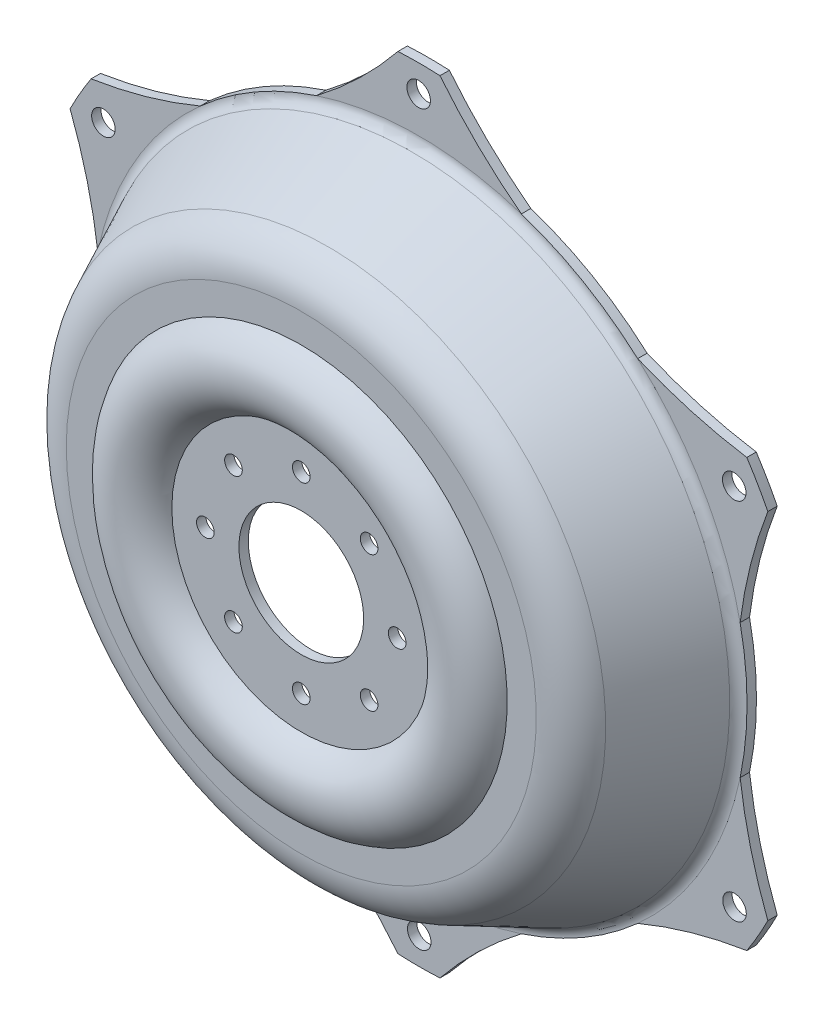
SolidWorks part; units mm, degrees
ref_plane "Front Plane" through (0, 0, 0) normal (0, 0, 1) x (1, 0, 0)
ref_plane "Top Plane" through (0, 0, 0) normal (0, 1, 0) x (1, 0, 0)
ref_plane "Right Plane" through (0, 0, 0) normal (1, 0, 0) x (0, 0, -1)
sketch "Sketch3" plane through (0, 0, 0) normal (0, 1, 0) x (1, 0, 0)
  line L16 (332.5, 100) -> (278.8208, 100)
  line L17 (262.5618, 89.723) -> (228.6217, 18.2702)
  line L18 (199.7168, 0) -> (169.6339, 0)
  line L19 (332.5, 92) -> (278.8208, 92)
  line L20 (269.788, 86.2906) -> (235.8479, 14.8377)
  line L21 (199.7168, -8) -> (175, -8)
  line L22 (0, 0) -> (0, -73.2185) construction
  line L23 (115.3661, 0) -> (53, 0)
  line L25 (53, -8) -> (53, 0)
  line L26 (324.5, 100) -> (278.8208, 100) construction
  line L27 (115.3661, 0) -> (61, 0) construction
  line L28 (110, -8) -> (53, -8)
  line L31 (332.5, 92) -> (332.5, 100)
  line L32 (61, 0) -> (61, 0) construction
  line L33 (324.5, 100) -> (324.5, 100) construction
  arc A6 (235.8479, 14.8377) -> (199.7168, -8) centre (199.7168, 32) cw
  arc A7 (269.788, 86.2906) -> (278.8208, 92) centre (278.8208, 82) cw
  arc A8 (262.5618, 89.723) -> (278.8208, 100) centre (278.8208, 82) cw
  arc A9 (228.6217, 18.2702) -> (199.7168, 0) centre (199.7168, 32) cw
  arc A10 (110, -8) -> (175, -8) centre (142.5, 8.4062) ccw
  arc A11 (115.3661, 0) -> (169.6339, 0) centre (142.5, 8.4062) ccw
  point P0 (142.5, -28)
  point P4 (225, -8)
  point P10 (272.5, 92)
  dimension "D8" = 20
  dimension "D9" = 40
  dimension "D10" = 10
  dimension "D1" = 53
  dimension "D2" = 110
  dimension "D3" = 175
  dimension "D4" = 50
  dimension "D5" = 100
  dimension "D6" = 60
  dimension "D7" = 89.5
  dimension "D11" = 8
  dimension "D13" = 47.5
  dimension "D12" = 8
revolve "Revolve1" add sketch "Sketch3" angle 360 about L22
sketch "Sketch5" plane through (0, 0, -100) normal (0, 0, 1) x (1, 0, 0)
  line L0 (0, 0) -> (0, 332.5) construction
  circle A0 centre (0, 0) radius 332.5 construction
  circle A1 centre (267.9147, 154.9582) radius 10
  arc A2 (296.4614, 150.5553) -> (269.8116, 0) centre (669.7531, 6.8428) ccw
  arc A3 (296.4614, 150.5553) -> (278.6154, 181.4654) centre (0, 0) ccw
  arc A4 (134.9058, 233.6637) -> (278.6154, 181.4654) centre (340.8025, 576.6018) ccw
  circle A5 centre (268.155, -154.5418) radius 10
  arc A6 (278.6154, -181.4654) -> (134.9058, -233.6637) centre (340.8025, -576.6018) ccw
  arc A7 (278.6154, -181.4654) -> (296.4614, -150.5553) centre (0, 0) ccw
  arc A8 (269.8116, 0) -> (296.4614, -150.5553) centre (669.7531, -6.8428) ccw
  circle A9 centre (0.2404, -309.5) radius 10
  arc A10 (-17.8459, -332.0207) -> (-134.9058, -233.6637) centre (-328.9505, -583.4445) ccw
  arc A11 (-17.8459, -332.0207) -> (17.8459, -332.0207) centre (0, 0) ccw
  arc A12 (134.9058, -233.6637) -> (17.8459, -332.0207) centre (328.9505, -583.4445) ccw
  circle A13 centre (-267.9147, -154.9582) radius 10
  arc A14 (17.8459, 332.0207) -> (134.9058, 233.6637) centre (328.9505, 583.4445) ccw
  arc A15 (17.8459, 332.0207) -> (-17.8459, 332.0207) centre (0, 0) ccw
  arc A16 (-134.9058, 233.6637) -> (-17.8459, 332.0207) centre (-328.9505, 583.4445) ccw
  circle A17 centre (-0.2404, 309.5) radius 10
  arc A18 (-296.4614, -150.5553) -> (-269.8116, 0) centre (-669.7531, -6.8428) ccw
  arc A19 (-296.4614, -150.5553) -> (-278.6154, -181.4654) centre (0, 0) ccw
  arc A20 (-134.9058, -233.6637) -> (-278.6154, -181.4654) centre (-340.8025, -576.6018) ccw
  circle A21 centre (-268.155, 154.5418) radius 10
  circle A22 centre (0, 0) radius 269.788 construction
  arc A25 (-278.6154, 181.4654) -> (-134.9058, 233.6637) centre (-340.8025, 576.6018) ccw
  arc A26 (-278.6154, 181.4654) -> (-296.4614, 150.5553) centre (0, 0) ccw
  arc A27 (-269.8116, 0) -> (-296.4614, 150.5553) centre (-669.7531, 6.8428) ccw
  circle A28 centre (0, 0) radius 332.5
  circle M31 centre (0, 0) radius 278.8208
  circle M32 centre (0, 0) radius 332.5
  dimension "D1" = 400
  dimension "D2" = 400
  dimension "D3" = 269.8116
  dimension "D4" = 20
  dimension "D5" = 23
  dimension "D6" = 6
extrude "Cut-Extrude2" cut sketch "Sketch5" along normal through all contours A27 A18 M31 M32 | A25 A16 M32 M31 | A14 A4 M32 M31 | A8 A2 M31 M32 | A12 A6 M31 M32 | A20 A10 M31 M32 | A21 | A17 | A1 | A5 | A9 | A13
hole_wizard "Ø15.0 (15) Diameter Hole1" positions "Sketch7" profile "Sketch6" hole size "Ø15.0" standard "Ansi Metric"
sketch "Sketch7" plane through (0, 0, 8) normal (0, 0, 1) x (1, 0, 0)
  line L0 (0, 110) -> (0, 53) construction
  circle A0 centre (0, 0) radius 110 construction
  circle A1 centre (0, 0) radius 53 construction
  point P0 (0, 81.5)
  point P20 (57.6292, 57.6292)
  point P21 (81.5, 0)
  point P22 (57.6292, -57.6292)
  point P23 (0, -81.5)
  point P24 (-57.6292, -57.6292)
  point P25 (-81.5, 0)
  point P26 (-57.6292, 57.6292)
  dimension "D1" = 8
sketch "Sketch6" plane through (0, 81.5, 8) normal (1, 0, 0) x (0, -1, 0)
  line L0 (0, 0) -> (0, 60.1065)
  line L1 (0, 60.1065) -> (7.5, 55.6)
  line L2 (7.5, 55.6) -> (7.5, 0)
  line L5 (7.5, 0) -> (0, 0)
  line L10 (0, 60.1065) -> (-7.5, 55.6) construction
  line L11 (0, -6.35) -> (0, 107.95) construction
  dimension "Hole Dia." = 15
  dimension "Hole Depth" = 55.6
  dimension "Drill Angle" = 118
